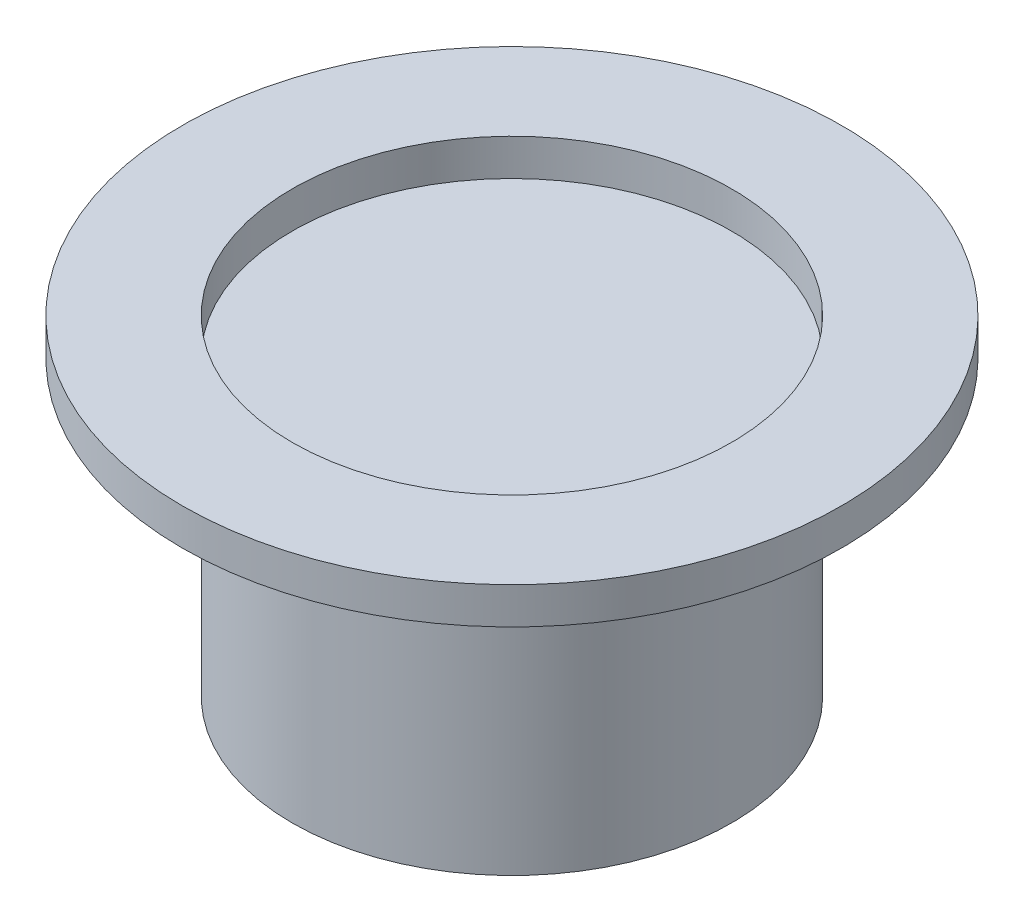
SolidWorks part; units mm, degrees
ref_plane "Alzado" through (0, 0, 0) normal (0, 0, 1) x (1, 0, 0)
ref_plane "Planta" through (0, 0, 0) normal (0, 1, 0) x (1, 0, 0)
ref_plane "Vista lateral" through (0, 0, 0) normal (1, 0, 0) x (0, 0, -1)
sketch "Croquis1" plane through (0, 0, 0) normal (0, 1, 0) x (1, 0, 0)
  circle A0 centre (0, 0) radius 3
extrude "Saliente-Extruir1" add sketch "Croquis1" along normal blind 4
sketch "Croquis2" plane through (0, 4, 0) normal (0, 1, 0) x (1, 0, 0)
  circle A0 centre (0, 0) radius 4.5
  circle A1 centre (0, 0) radius 3 construction
  circle A2 centre (0, 0) radius 3
extrude "Saliente-Extruir2" add sketch "Croquis2" along normal blind 0.5 separate body
